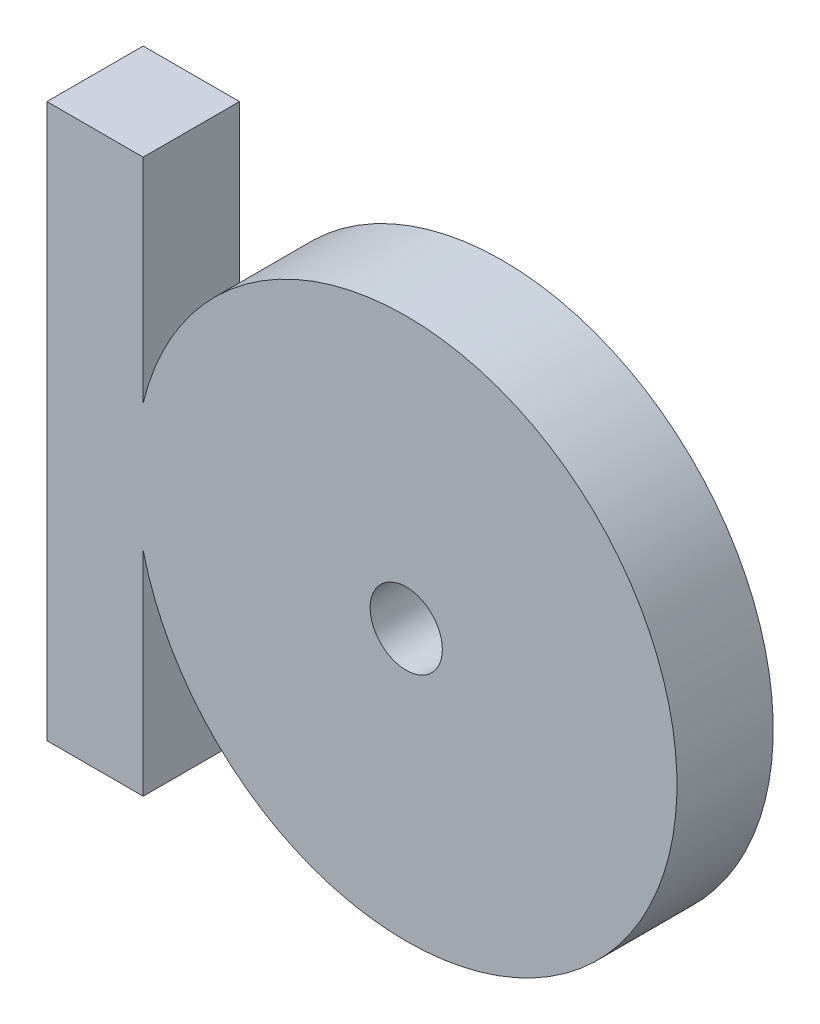
SolidWorks part; units mm, degrees
ref_plane "Спереди" through (0, 0, 0) normal (0, 0, 1) x (1, 0, 0)
ref_plane "Сверху" through (0, 0, 0) normal (0, 1, 0) x (1, 0, 0)
ref_plane "Справа" through (0, 0, 0) normal (1, 0, 0) x (0, 0, -1)
sketch "Эскиз1" plane through (0, 0, 0) normal (0, 0, 1) x (1, 0, 0)
  line L0 (4, 0) -> (4, 8.8415)
  line L1 (0, 0) -> (4, 0)
  line L2 (0, 0) -> (0, 23)
  line L3 (0, 23) -> (4, 23)
  line L5 (4, 14.1585) -> (4, 23)
  arc A4 (4, 8.8415) -> (4, 14.1585) centre (14.9314, 11.5) ccw
  circle A5 centre (14.9314, 11.5) radius 1.5
  dimension "D3" = 3
  dimension "D4" = 22.5
  dimension "D1" = 23
  dimension "D2" = 4
extrude "Бобышка-Вытянуть1" add sketch "Эскиз1" along normal blind 4
